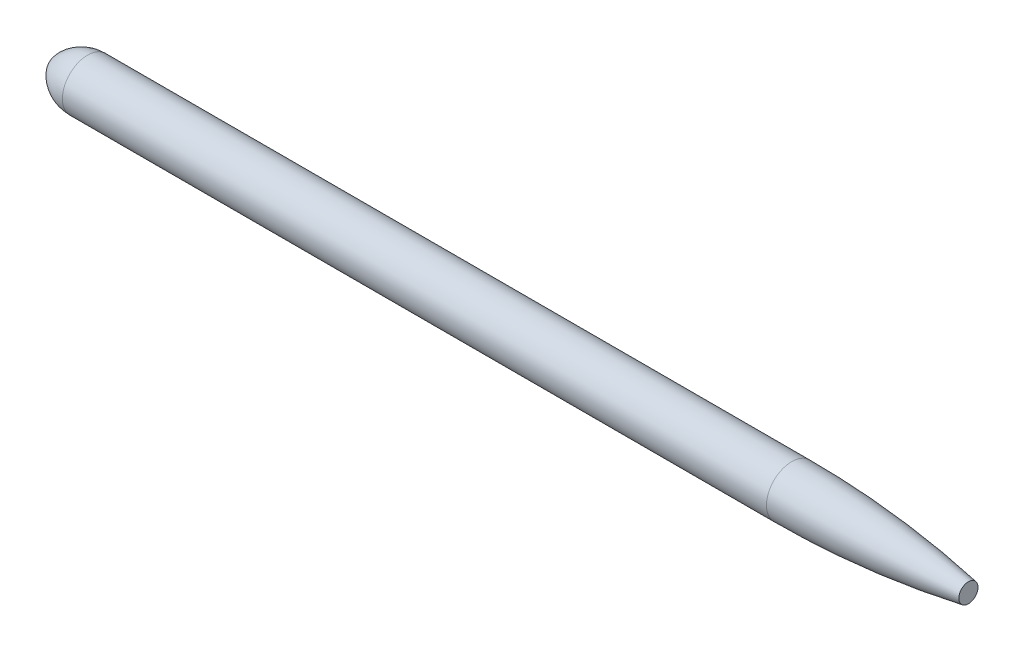
SolidWorks part; units mm, degrees
ref_plane "Front Plane" through (0, 0, 0) normal (0, 0, 1) x (1, 0, 0)
ref_plane "Top Plane" through (0, 0, 0) normal (0, 1, 0) x (1, 0, 0)
ref_plane "Right Plane" through (0, 0, 0) normal (1, 0, 0) x (0, 0, -1)
sketch "Sketch1" plane through (0, 0, 0) normal (0, 0, 1) x (1, 0, 0)
  line L1 (270, 184.1699) -> (5410, 184.1699)
  line L2 (6700, 70) -> (6700, 0)
  line L3 (6700, 0) -> (0, 0)
  arc A0 (5410, 184.1699) -> (6700, 70) centre (5410, -7160.7348) cw
  arc A1 (270, 184.1699) -> (0, 0) centre (270, -105.8301) ccw
  dimension "D1" = 290
  dimension "D2" = 270
  dimension "D3" = 6700
  dimension "D4" = 70
  dimension "D5" = 1290
  dimension "D6" = 184.1699
revolve "Revolve1" add sketch "Sketch1" angle 360 about L3
